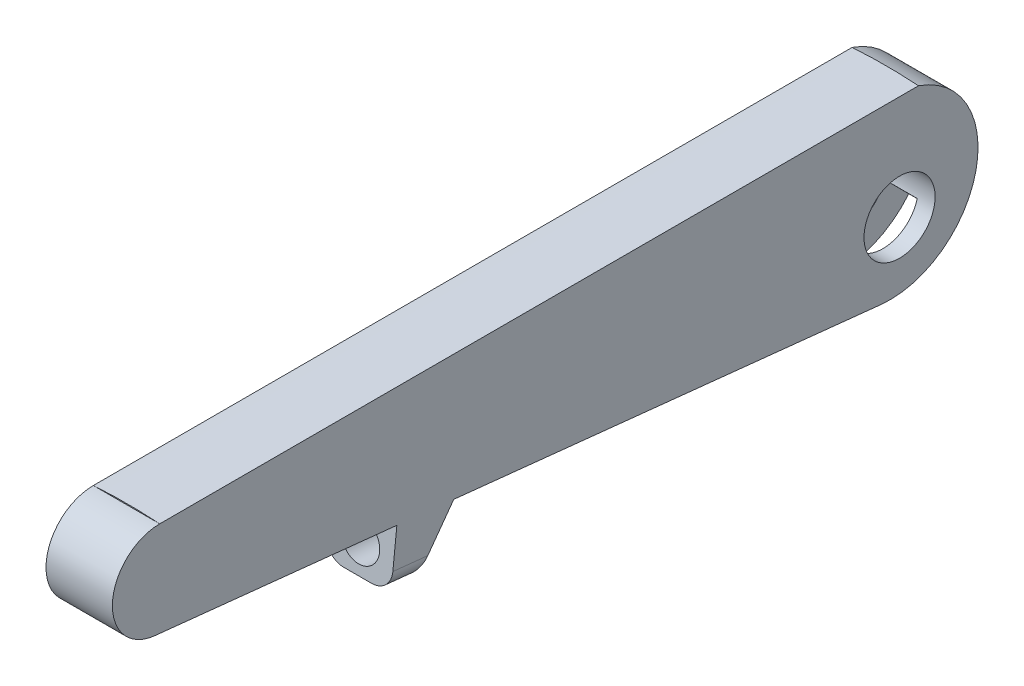
SolidWorks part; units mm, degrees
ref_plane "Front Plane" through (0, 0, 0) normal (0, 0, 1) x (1, 0, 0)
ref_plane "Top Plane" through (0, 0, 0) normal (0, 1, 0) x (1, 0, 0)
ref_plane "Right Plane" through (0, 0, 0) normal (1, 0, 0) x (0, 0, -1)
sketch "Sketch1" plane through (0, 0, 0) normal (1, 0, 0) x (0, 0, -1)
  line L0 (0, 0) -> (-80, 0)
  line L1 (-80.5217, -9.954) -> (-3.9695, -18)
  line L2 (-55, -12.6365) -> (-55.6306, -18.6365)
  line L3 (-53.0947, -18.903) -> (-49, -13.2671)
  line L4 (-55.6306, -18.6365) -> (-53.0947, -18.903)
  arc A0 (-80, 0) -> (-80.5217, -9.954) centre (-80, -4.9907) ccw
  arc A1 (-3.9695, -18) -> (0, 0) centre (-3, -8.7761) ccw
  circle A2 centre (-2, -11) radius 3.75
  dimension "D5" = 7.5
  dimension "D9" = 60
  dimension "D10" = 6
  dimension "D1" = 6
  dimension "D2" = 80
  dimension "D3" = 18
  dimension "D4" = 3
  dimension "D6" = 11
  dimension "D7" = 2
  dimension "D8" = 6
  dimension "D11" = 25
extrude "Boss-Extrude1" add sketch "Sketch1" along normal mid plane 7 contours L1 A1 L0 A0 A2 | L2 L4 L3 L1
ref_plane "Plane1" through (0, -37.6202, 27.3327) normal (0, -0.809, 0.5878) x (-1, 0, 0)
sketch "Sketch3" plane through (0, -37.6202, 27.3327) normal (0, -0.809, 0.5878) x (-1, 0, 0)
  line L0 (-3.5, -31.8436) -> (3.5, -31.8436) construction
  line L1 (-3.5, -31.8436) -> (3.5, -31.8436)
  line L2 (-3.5, -31.8436) -> (-3.5, -28.8436)
  line L3 (3.5, -31.8436) -> (3.5, -28.8436)
  arc A0 (-3.5, -28.8436) -> (3.5, -28.8436) centre (0, -28.8436) cw
  circle A1 centre (0, -28.8436) radius 2.5
  dimension "D1" = 1
  dimension "D2" = 3
sketch "Sketch6" plane through (0, 0, 0) normal (1, 0, 0) x (0, 0, -1)
  line L0 (-2.9604, -7.3751) -> (-31.9599, -15.0581)
  line L1 (-49, -13.2671) -> (-3.9695, -18) construction
  line L2 (1.6195, -11.9808) -> (4.2208, -14.5968)
  line L9 (-80.5217, -9.954) -> (-55, -12.6365)
  line L15 (-55, -12.6365) -> (-55.6306, -18.6365)
  line L17 (0, 0) -> (-80, 0)
  line L26 (0, 0) -> (-80, 0)
  line L27 (-55.6306, -18.6365) -> (-53.0947, -18.903)
  line L31 (-53.0947, -18.903) -> (-49, -13.2671)
  line L32 (-49, -13.2671) -> (-3.9695, -18)
  line L33 (-49, -13.2671) -> (-3.9695, -18)
  circle A0 centre (-2, -11) radius 3.75 construction
  circle A1 centre (-2, -11) radius 3.75
  arc A2 (-3.9695, -18) -> (0, 0) centre (-3, -8.7761) ccw
  arc A3 (-80, 0) -> (-80.5217, -9.954) centre (-80, -4.9907) ccw
  arc A4 (-3.9695, -18) -> (0, 0) centre (-3, -8.7761) ccw
  dimension "D2" = 30
  dimension "D3" = 120
  dimension "D1" = 0
extrude "Cut-Extrude1" cut sketch "Sketch6" against normal mid plane 3.5 contours L33 A4 L2 A1 L0
sketch "Sketch7" plane through (0, -6.1585, -1.6316) normal (0, -0.9667, -0.2561) x (1, 0, 0)
  line L0 (-1.436, 4.7504) -> (-1.436, 36.788)
  line L1 (-1.436, 36.788) -> (-0.936, 34.7504)
  line L2 (-0.936, 34.7504) -> (-0.936, 4.7504)
  line L3 (-0.936, 4.7504) -> (-1.436, 4.7504)
  line L4 (1.75, 4.7504) -> (1.75, 34.7504)
  line L5 (1.75, 34.7504) -> (-1.75, 34.7504)
  line L6 (-1.75, 34.7504) -> (-1.75, 4.7504)
  line L7 (-1.75, 4.7504) -> (1.75, 4.7504)
  line L8 (1.75, 4.7504) -> (1.75, 34.7504)
  line L9 (1.75, 34.7504) -> (-1.75, 34.7504)
  line L10 (-1.75, 34.7504) -> (-1.75, 4.7504)
  line L11 (-1.75, 4.7504) -> (1.75, 4.7504)
  dimension "D2" = 0.5
  dimension "D3" = 30
  dimension "D1" = 0
sketch "Sketch8" plane through (0, 0, 0) normal (0, 0, 1) x (1, 0, 0)
  line L0 (3.5, 0) -> (-3.5, 0) construction
  line L1 (3.5, 0) -> (-3.5, 0)
  circle A0 centre (0, -50.6793) radius 50.8
  dimension "D1" = 101.6
extrude "Boss-Extrude3" add sketch "Sketch8" along normal up to vertex (80 mm away) contours L1 A0
ref_plane "Plane2" through (10, 0, 0) normal (1, 0, 0) x (0, 0, -1)
sketch "Sketch9" plane through (0, 5.5795, 53.0854) normal (0, 0.1045, 0.9945) x (1, 0, 0)
  line L4 (-3.5, -18.3163) -> (-3.5, -24.3494)
  line L5 (-3.5, -24.3494) -> (3.5, -24.3494)
  line L6 (3.5, -24.3494) -> (3.5, -18.3163)
  line L7 (3.5, -18.3163) -> (-3.5, -18.3163)
  line L8 (-3.5, -18.3163) -> (-3.5, -24.3494)
  line L9 (-3.5, -24.3494) -> (3.5, -24.3494)
  line L10 (3.5, -24.3494) -> (3.5, -18.3163)
  line L11 (3.5, -18.3163) -> (-3.5, -18.3163)
  circle A0 centre (0, -21.3494) radius 2
  point P7 (0, -18.3163)
  dimension "D3" = 4
  dimension "D2" = 3
  dimension "D1" = 0
extrude "Cut-Extrude3" cut sketch "Sketch9" against normal blind 7 contours A0
fillet "Fillet2" radius 2 2 edges at (-3.5, -18.7697, 54.3627) (3.5, -18.7697, 54.3627)
sketch "Sketch10" plane through (1.75, 0, 0) normal (-1, 0, 0) x (0, 0, 1)
  line L3 (31.8863, -14.3581) -> (16.8863, -15.9347)
  line L4 (16.8863, -15.9347) -> (16.9599, -16.6347)
  line L5 (31.8863, -14.3581) -> (31.9599, -15.0581)
  line L6 (3.9695, -18) -> (31.9599, -15.0581)
  line L7 (31.9599, -15.0581) -> (2.9604, -7.3751)
  line L8 (-1.6195, -11.9808) -> (-4.2208, -14.5968)
  line L9 (3.9695, -18) -> (31.9599, -15.0581)
  line L10 (31.9599, -15.0581) -> (2.9604, -7.3751)
  line L11 (-1.6195, -11.9808) -> (-4.2208, -14.5968)
  arc A4 (-1.6195, -11.9808) -> (2.9604, -7.3751) centre (2, -11) ccw
  arc A5 (-4.2208, -14.5968) -> (3.9695, -18) centre (3, -8.7761) ccw
  arc A6 (-1.6195, -11.9808) -> (2.9604, -7.3751) centre (2, -11) ccw
  arc A7 (-4.2208, -14.5968) -> (3.9695, -18) centre (3, -8.7761) ccw
  line M8 (3.9695, -18) -> (31.9599, -15.0581)
  line M9 (31.9599, -15.0581) -> (2.9604, -7.3751)
  dimension "D2" = 15
  dimension "D3" = 0.7
  dimension "D1" = 0
extrude "Boss-Extrude7" add sketch "Sketch10" along normal up to surface (3.5 mm away) contours L3 L4 M8 M9 | L5 L3 M9 up to face at (-1.75, -14.4039, 7.321)
